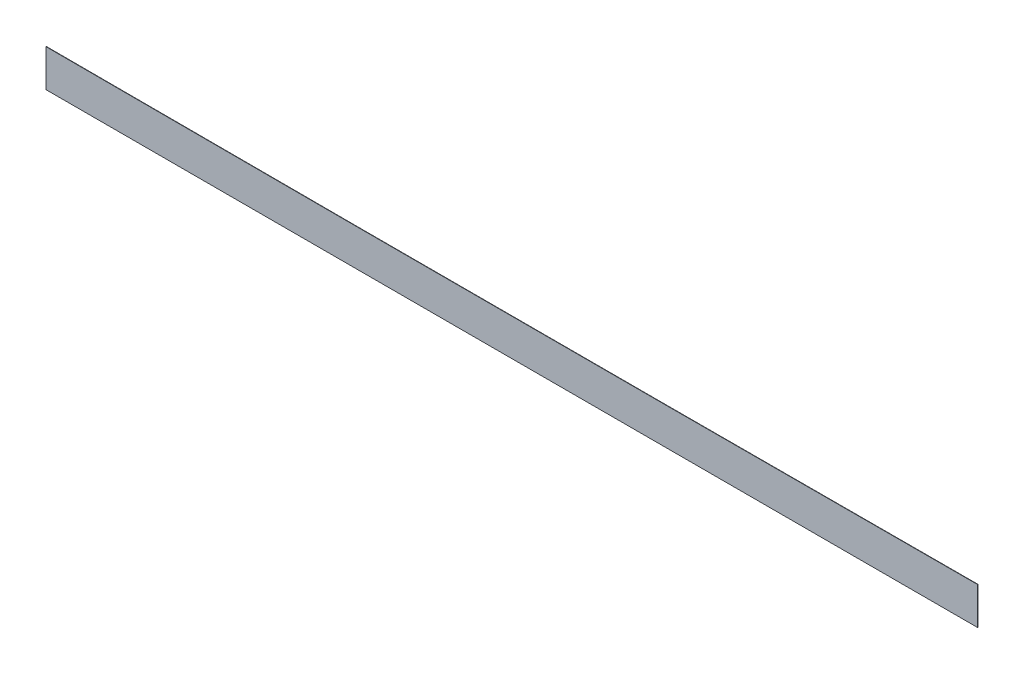
SolidWorks part; units mm, degrees
ref_plane "vorne" through (0, 0, 0) normal (0, 0, 1) x (1, 0, 0)
ref_plane "oben" through (0, 0, 0) normal (0, 1, 0) x (1, 0, 0)
ref_plane "rechts" through (0, 0, 0) normal (1, 0, 0) x (0, 0, -1)
sketch "Skizze1" plane through (0, 0, 0) normal (0, 0, 1) x (1, 0, 0)
  line L0 (0, 0) -> (0, 98.5) construction
  line L6 (-1250, 100) -> (-1250, 0)
  line L7 (-1250, 0) -> (1250, 0)
  line L8 (1250, 100) -> (1250, 0)
  arc A2 (-1250, 100) -> (1250, 100) centre (0, 520932.5833) ccw
  dimension "D3" = 2500
  dimension "D4" = 98.5
  dimension "D1" = 520834.0833
  dimension "D2" = 100
extrude "Aufsatz-Linear austragen1" add sketch "Skizze1" along normal blind 1
